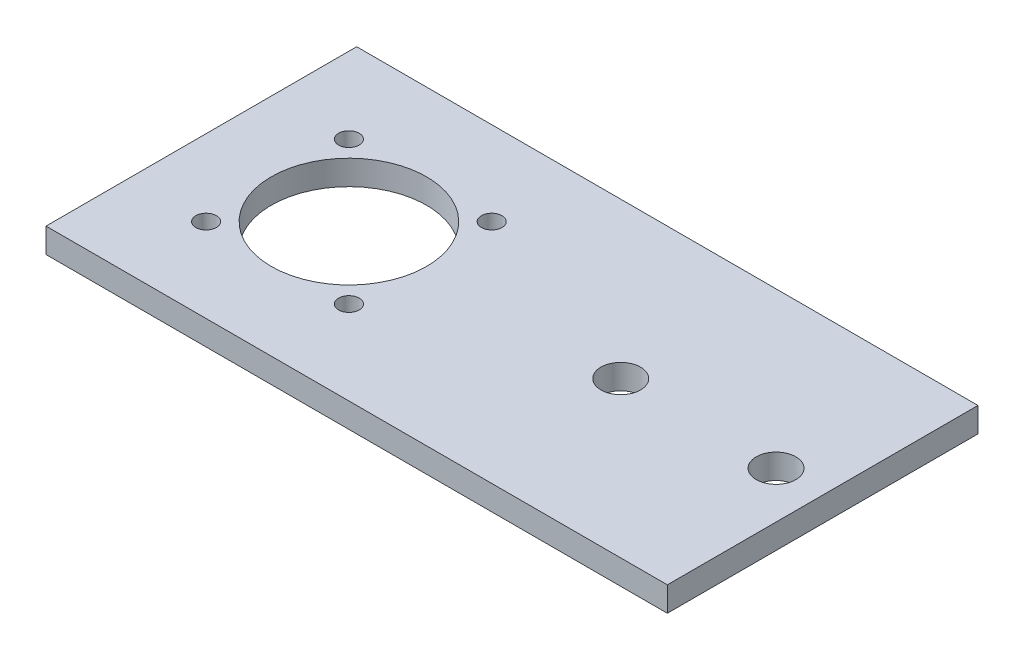
SolidWorks part; units mm, degrees
ref_plane "Front Plane" through (0, 0, 0) normal (0, 0, 1) x (1, 0, 0)
ref_plane "Top Plane" through (0, 0, 0) normal (0, 1, 0) x (1, 0, 0)
ref_plane "Right Plane" through (0, 0, 0) normal (1, 0, 0) x (0, 0, -1)
sketch "Sketch1" plane through (0, 0, 0) normal (0, 1, 0) x (1, 0, 0)
  line L1 (0, 0) -> (80, 0)
  line L2 (0, 0) -> (0, 40)
  line L3 (0, 40) -> (80, 40)
  line L4 (80, 0) -> (80, 40)
  line L5 (31.557, 23.3646) -> (22.3646, 32.557) construction
  line L6 (22.3646, 32.557) -> (9.8076, 29.1924) construction
  line L7 (9.8076, 29.1924) -> (6.443, 16.6354) construction
  line L8 (6.443, 16.6354) -> (15.6354, 7.443) construction
  line L9 (15.6354, 7.443) -> (28.1924, 10.8076) construction
  line L10 (28.1924, 10.8076) -> (31.557, 23.3646) construction
  circle A0 centre (54, 20) radius 2.55
  circle A1 centre (74, 20) radius 2.55
  circle A2 centre (19, 20) radius 11.2583 construction
  circle A3 centre (19, 20) radius 10
  circle A4 centre (28.1924, 10.8076) radius 1.325
  circle A5 centre (19, 20) radius 11.2583 construction
  circle A6 centre (9.8076, 10.8076) radius 1.325
  circle A7 centre (19, 20) radius 11.2583 construction
  circle A8 centre (9.8076, 29.1924) radius 1.325
  circle A9 centre (19, 20) radius 11.2583 construction
  circle A10 centre (28.1924, 29.1924) radius 1.325
  point P20 (0, 20)
  point P38 (19, 20)
  dimension "D3" = 5.1
  dimension "D4" = 20
  dimension "D7" = 20
  dimension "D9" = 2.65
  dimension "D1" = 40
  dimension "D2" = 80
  dimension "D5" = 6
  dimension "D6" = 15
  dimension "D8" = 26
  dimension "D11" = 19
  dimension "D10" = 4
extrude "Boss-Extrude1" add sketch "Sketch1" along normal blind 3.175
